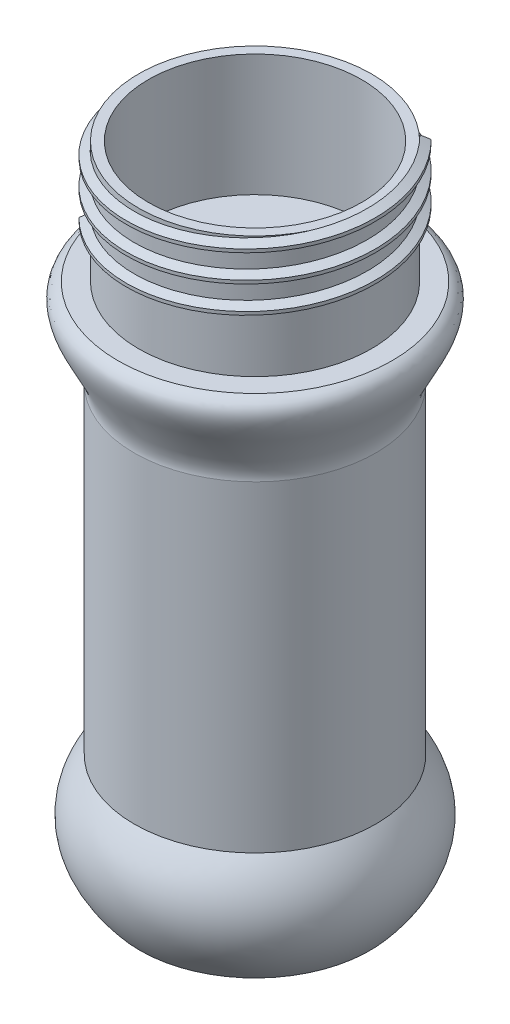
SolidWorks part; units mm, degrees
ref_plane "Спереди" through (0, 0, 0) normal (0, 0, 1) x (1, 0, 0)
ref_plane "Сверху" through (0, 0, 0) normal (0, 1, 0) x (1, 0, 0)
ref_plane "Справа" through (0, 0, 0) normal (1, 0, 0) x (0, 0, -1)
sketch "Эскиз1" plane through (0, 0, 0) normal (0, 1, 0) x (1, 0, 0)
  circle A0 centre (0, 0) radius 20.25
  circle A1 centre (0, -20.25) radius 7.2898 construction
ref_plane "Плоскость1" through (0, 0, 20.25) normal (1, 0, 0) x (0, 0, -1)
sketch "Эскиз2" plane through (0, 0, 20.25) normal (1, 0, 0) x (0, 0, -1)
  line L0 (20.25, -2.8848) -> (20.25, 13.7152)
  line L1 (3.25, -2.8848) -> (20.25, -2.8848)
  line L2 (20.25, 13.7152) -> (2.4, 13.7152)
  spline S0 degree 2 poles (3.25, -2.8848) (-4.1403, 5.7214) (2.4, 13.7152) knots 0 0 0 1 1 1
sweep "По траектории5" add profiles "Эскиз2" path "Эскиз1"
sketch "Эскиз3" plane through (0, 13.7152, 0) normal (0, 1, 0) x (1, 0, 0)
  circle A0 centre (0, 0) radius 17.85
extrude "Бобышка-Вытянуть1" add sketch "Эскиз3" along normal blind 47.5
sketch "Эскиз4" plane through (0, 0, 20.25) normal (1, 0, 0) x (0, 0, -1)
  line L0 (2.4, 13.7152) -> (2.4, 61.2152) construction
  line L1 (2.4, 61.2152) -> (2.4, 74.2152) construction
  line L2 (2.4, 61.2152) -> (38.1, 61.2152) construction
  line L3 (20.25, 61.2152) -> (20.25, 74.2152)
  line L4 (20.25, 74.2152) -> (0, 74.2152)
  line L5 (20.25, 61.2152) -> (2.4, 61.2152)
  line L6 (2.4, 61.2152) -> (2.3956, 61.1791)
  spline S0 degree 3 poles (2.4, 61.2152) (3.0081, 65.1516) (-4.6864, 72.1185) (0, 74.2152) knots 0 0 0 0 1 1 1 1
ref_plane "Плоскость2" through (0, 66.2152, 0) normal (0, 1, 0) x (1, 0, 0)
revolve "Повернуть1" add sketch "Эскиз4" angle 360 about L3
sketch "Эскиз5" plane through (0, 74.2152, 0) normal (0, 1, 0) x (1, 0, 0)
  circle A0 centre (0, 0) radius 15.75
  circle A1 centre (0, 0) radius 17.2
extrude "Бобышка-Вытянуть2" add sketch "Эскиз5" along normal blind 18
sketch "Эскиз8" plane through (0, 92.2152, 0) normal (0, 1, 0) x (1, 0, 0)
  circle A0 centre (0, 0) radius 17.2
curve "Спираль1" pitch 4 height 10 turns 2.5
ref_plane "Плоскость4" through (12.1622, 92.2152, -12.1622) normal (0.7066, -0.037, 0.7066) x (0.7057, -0.037, -0.7076)
sketch "Эскиз9" plane through (12.1622, 92.2152, -12.1622) normal (0.7066, -0.037, 0.7066) x (0.7057, -0.037, -0.7076)
  line L0 (0, 0.8037) -> (0, -0.8037)
  line L1 (0, 0) -> (1.2, 0) construction
  line L2 (1.2, -0.25) -> (0, -0.8037)
  line L3 (1.2, -0.25) -> (1.2, 0.25)
  line L4 (1.2, 0.25) -> (0, 0.8037)
  circle A0 centre (0, 0) radius 0.8037 construction
  circle A1 centre (1.2, 0) radius 0.25 construction
sweep "По траектории6" add profiles "Эскиз9" path "Спираль1"
